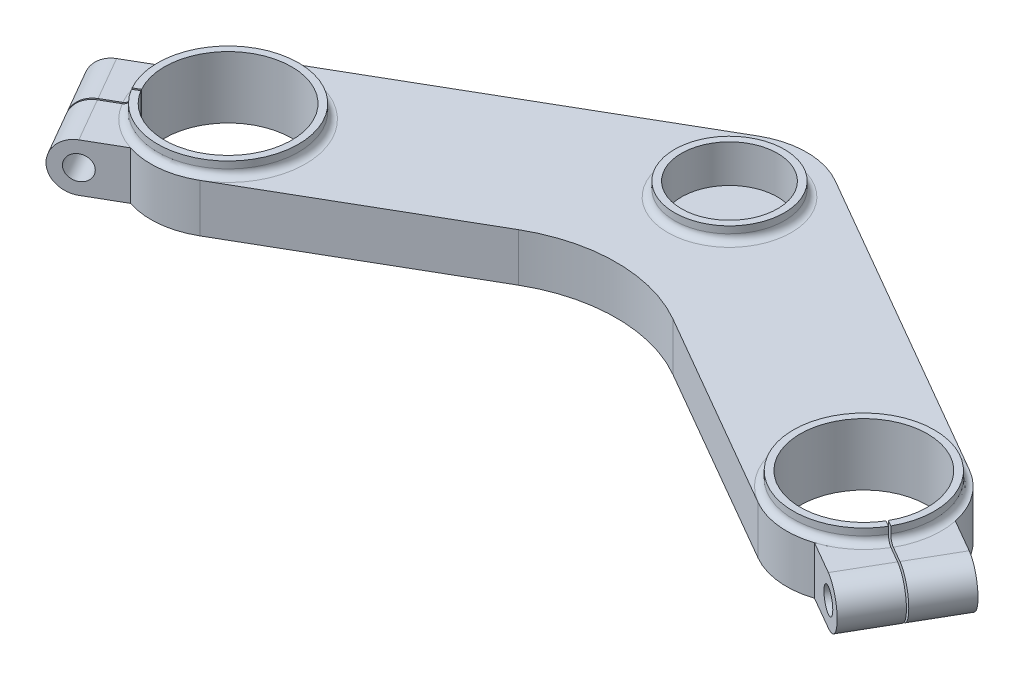
SolidWorks part; units mm, degrees
ref_plane "Front Plane" through (0, 0, 0) normal (0, 0, 1) x (1, 0, 0)
ref_plane "Top Plane" through (0, 0, 0) normal (0, 1, 0) x (1, 0, 0)
ref_plane "Right Plane" through (0, 0, 0) normal (1, 0, 0) x (0, 0, -1)
sketch "Sketch1" plane through (0, 0, 0) normal (0, 1, 0) x (1, 0, 0)
  line L14 (0, 0) -> (-92.5, -53.4049) construction
  line L15 (0, 0) -> (92.5, -53.4049) construction
  line L16 (0, -25.9808) -> (0, -80.2974) construction
  line L17 (-103.75, -33.9193) -> (-11.25, 19.4856)
  line L18 (-81.25, -72.8905) -> (0, -25.9808)
  line L19 (11.25, 19.4856) -> (103.75, -33.9193)
  line L20 (0, -25.9808) -> (81.25, -72.8905)
  line L21 (0, -25.9808) -> (11.25, -19.4856) construction
  line L22 (0, -25.9808) -> (-11.25, -19.4856) construction
  line L23 (-92.5, -53.4049) -> (92.5, -53.4049) construction
  arc A1 (-103.75, -33.9193) -> (-81.25, -72.8905) centre (-92.5, -53.4049) ccw
  arc A2 (81.25, -72.8905) -> (103.75, -33.9193) centre (92.5, -53.4049) ccw
  arc A3 (11.25, 19.4856) -> (-11.25, 19.4856) centre (0, 0) ccw
  circle A4 centre (0, 0) radius 22.5 construction
  dimension "D1" = 45
  dimension "D2" = 185
  dimension "D3" = 60
  dimension "D6" = 45
  dimension "D7" = 45
  dimension "D4" = 60
extrude "Boss-Extrude1" add sketch "Sketch1" along normal blind 14 contours L19 A2 L20 L18 A1 L17 A3
fillet "Fillet2" radius 45 1 edges at (0, 7, 25.9808)
sketch "Sketch2" plane through (0, 14, 0) normal (0, 1, 0) x (1, 0, 0)
  circle A0 centre (-92.5, -53.4049) radius 18.51
  circle A1 centre (92.5, -53.4049) radius 18.51
  dimension "D1" = 37.02
  dimension "D2" = 37.02
extrude "Cut-Extrude1" cut sketch "Sketch2" against normal through all
sketch "Sketch3" plane through (0, 14, 0) normal (0, 1, 0) x (1, 0, 0)
  circle A0 centre (0, 0) radius 13.985
  dimension "D1" = 27.97
extrude "Cut-Extrude2" cut sketch "Sketch3" against normal blind 7
sketch "Sketch4" plane through (0, 14, 0) normal (0, 1, 0) x (1, 0, 0)
  line L0 (-114.5237, -48.7998) -> (-131.8442, -58.7998)
  line L1 (-131.8442, -58.7998) -> (-116.8442, -84.7805)
  line L2 (-116.8442, -84.7805) -> (-99.5237, -74.7805)
  line L3 (-103.75, -33.9193) -> (-11.25, 19.4856) construction
  line L4 (-124.3442, -71.7902) -> (-92.5, -53.4049) construction
  line L5 (0, 0) -> (-92.5, -53.4049) construction
  line L6 (-114.5237, -48.7998) -> (-99.5237, -74.7805) construction
  line L7 (0, 0) -> (0, -93.6137) construction
  line L8 (114.5237, -48.7998) -> (131.8442, -58.7998)
  line L9 (131.8442, -58.7998) -> (116.8442, -84.7805)
  line L10 (116.8442, -84.7805) -> (99.5237, -74.7805)
  arc A0 (-103.75, -33.9193) -> (-81.25, -72.8905) centre (-92.5, -53.4049) ccw construction
  arc A1 (-114.5237, -48.7998) -> (-99.5237, -74.7805) centre (-92.5, -53.4049) ccw
  arc A2 (99.5237, -74.7805) -> (114.5237, -48.7998) centre (92.5, -53.4049) ccw
  arc A3 (81.25, -72.8905) -> (103.75, -33.9193) centre (92.5, -53.4049) ccw construction
  point P19 (-124.3442, -71.7902)
  dimension "D1" = 20
  dimension "D2" = 30
extrude "Boss-Extrude2" add sketch "Sketch4" against normal blind 14
sketch "Sketch5" plane through (7.5, 0, 12.9904) normal (0.5, 0, 0.866) x (0.866, 0, -0.5)
  line L0 (-143.5803, 0) -> (-143.5803, 14)
  line L1 (-143.5803, 14) -> (-134.5803, 14)
  line L3 (-134.5803, 0) -> (-143.5803, 0)
  arc A0 (-134.5803, 14) -> (-134.5803, 0) centre (-134.5803, 7) ccw
  dimension "D1" = 7
  dimension "D2" = 9
  dimension "D3" = 9
extrude "Cut-Extrude3" cut sketch "Sketch5" against normal through all
sketch "Sketch6" plane through (-7.5, 0, 12.9904) normal (-0.5, 0, 0.866) x (0.866, 0, 0.5)
  line L8 (134.5803, 14) -> (143.5803, 14)
  line L9 (143.5803, 14) -> (143.5803, 0)
  line L10 (143.5803, 0) -> (134.5803, 0)
  arc A1 (134.5803, 14) -> (134.5803, 0) centre (134.5803, 7) cw
  dimension "D3" = 9
  dimension "D1" = 7
  dimension "D2" = 9
extrude "Cut-Extrude4" cut sketch "Sketch6" against normal through all
sketch "Sketch9" plane through (0, 14, 0) normal (0, 1, 0) x (1, 0, 0)
  circle A0 centre (-92.5, -53.4049) radius 18.51
  circle A1 centre (-92.5, -53.4049) radius 18.51 construction
  circle A2 centre (-92.5, -53.4049) radius 20.51
  circle A3 centre (0, 0) radius 13.985
  circle A4 centre (0, 0) radius 15.985
  circle A5 centre (0, 0) radius 13.985 construction
  circle A6 centre (92.5, -53.4049) radius 18.51
  circle A7 centre (92.5, -53.4049) radius 20.51
  circle A8 centre (92.5, -53.4049) radius 18.51 construction
  dimension "D1" = 2
  dimension "D2" = 2
  dimension "D3" = 2
extrude "Boss-Extrude3" add sketch "Sketch9" along normal blind 4
fillet "Fillet5" radius 2 3 edges at (-92.5, 14, 73.9149) (92.5, 14, 73.9149) (0, 14, 15.985)
sketch "Sketch10" plane through (7.5, 0, 12.9904) normal (0.5, 0, 0.866) x (0.866, 0, -0.5)
  circle A0 centre (-134.5803, 7) radius 3.5
  dimension "D1" = 7
extrude "Cut-Extrude5" cut sketch "Sketch10" against normal blind 42
sketch "Sketch11" plane through (-7.5, 0, 12.9904) normal (-0.5, 0, 0.866) x (0.866, 0, 0.5)
  circle A0 centre (134.5803, 7) radius 3.5
  dimension "D1" = 7
extrude "Cut-Extrude6" cut sketch "Sketch11" against normal blind 42
sketch "Sketch12" plane through (0, 18, 0) normal (0, 1, 0) x (1, 0, 0)
  line L0 (-92.3633, -53.6142) -> (-129.001, -74.767)
  line L1 (-103.75, -33.9193) -> (-11.25, 19.4856) construction
  line L2 (-92.6367, -53.1956) -> (-129.2744, -74.3484)
  line L3 (-92.6367, -53.1956) -> (-92.3633, -53.6142)
  line L4 (-129.2744, -74.3484) -> (-129.001, -74.767)
  line L5 (0, -9.9) -> (0, 9.9) construction
  line L6 (129.2744, -74.3484) -> (129.001, -74.767)
  line L7 (92.6367, -53.1956) -> (92.3633, -53.6142)
  line L8 (92.6367, -53.1956) -> (129.2744, -74.3484)
  line L9 (92.3633, -53.6142) -> (129.001, -74.767)
  point P6 (-92.5, -53.4049)
  dimension "D1" = 0.5
extrude "Cut-Extrude7" cut sketch "Sketch12" against normal blind 42
